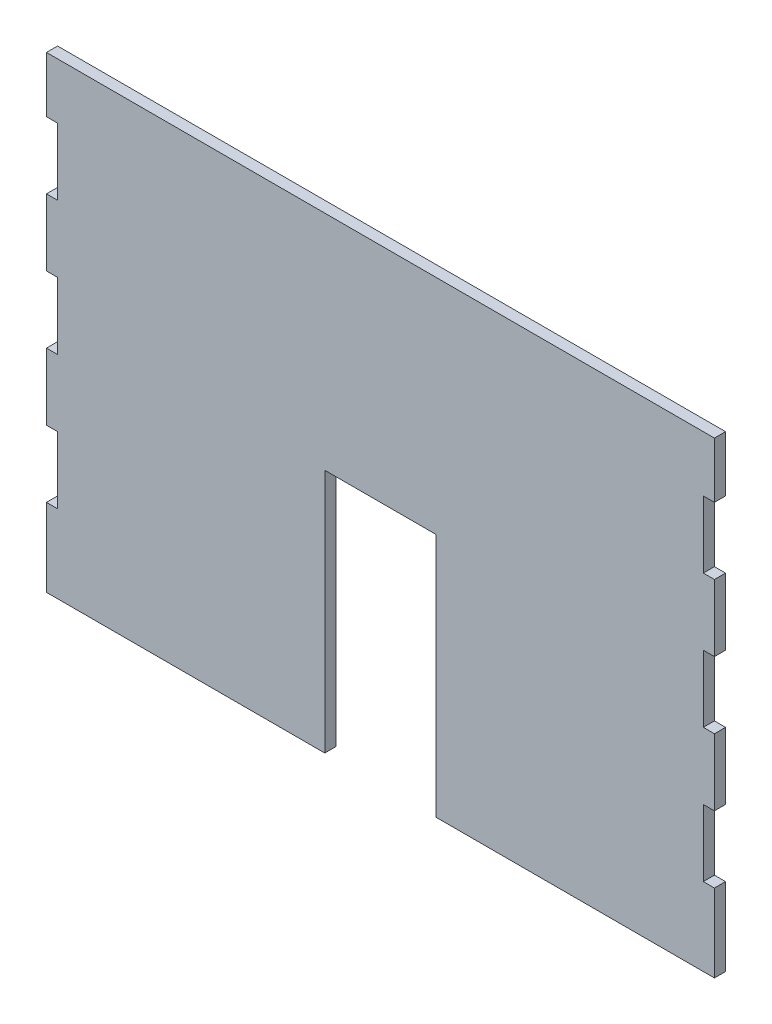
SolidWorks part; units mm, degrees
ref_plane "Front Plane" through (0, 0, 0) normal (0, 0, 1) x (1, 0, 0)
ref_plane "Top Plane" through (0, 0, 0) normal (0, 1, 0) x (1, 0, 0)
ref_plane "Right Plane" through (0, 0, 0) normal (1, 0, 0) x (0, 0, -1)
sketch "Sketch1" plane through (0, 0, 0) normal (0, 0, 1) x (1, 0, 0)
  line L1 (-150, 105) -> (150, 105)
  line L2 (-150, 105) -> (-150, -105)
  line L3 (-150, -105) -> (150, -105)
  line L4 (150, 105) -> (150, -105)
  line L5 (-150, 105) -> (150, -105) construction
  line L6 (-150, -105) -> (150, 105) construction
  point P0 (0, 0)
  dimension "D1" = 300
  dimension "D2" = 210
extrude "Boss-Extrude1" add sketch "Sketch1" along normal blind 5
sketch "Sketch2" plane through (0, 0, 0) normal (0, 0, -1) x (-1, 0, 0)
  line L0 (-150, 105) -> (150, 105) construction
  line L1 (-212.6198, 80) -> (-145, 80)
  line L2 (-212.6198, 80) -> (-212.6198, 50)
  line L3 (-212.6198, 50) -> (-145, 50)
  line L4 (-145, 80) -> (-145, 50)
  line L5 (-212.6198, 80) -> (-145, 50) construction
  line L6 (-212.6198, 50) -> (-145, 80) construction
  line L7 (-150, -105) -> (-150, 105) construction
  line L8 (-217.6198, 20) -> (-145, 20)
  line L9 (-217.6198, 20) -> (-217.6198, -10)
  line L10 (-217.6198, -10) -> (-145, -10)
  line L11 (-145, 20) -> (-145, -10)
  line L12 (-217.6198, 20) -> (-145, -10) construction
  line L13 (-217.6198, -10) -> (-145, 20) construction
  line L14 (-217.6198, -70) -> (-145, -70)
  line L15 (-217.6198, -70) -> (-217.6198, -40)
  line L16 (-217.6198, -40) -> (-145, -40)
  line L17 (-145, -70) -> (-145, -40)
  line L18 (-217.6198, -70) -> (-145, -40) construction
  line L19 (-217.6198, -40) -> (-145, -70) construction
  line L20 (150, 105) -> (150, -105) construction
  line L21 (145, 80) -> (198.2126, 80)
  line L22 (145, 80) -> (145, 50)
  line L23 (145, 50) -> (198.2126, 50)
  line L24 (198.2126, 80) -> (198.2126, 50)
  line L25 (145, 80) -> (198.2126, 50) construction
  line L26 (145, 50) -> (198.2126, 80) construction
  line L27 (145, 20) -> (217.6198, 20)
  line L28 (145, 20) -> (145, -10)
  line L29 (145, -10) -> (217.6198, -10)
  line L30 (217.6198, 20) -> (217.6198, -10)
  line L31 (145, 20) -> (217.6198, -10) construction
  line L32 (145, -10) -> (217.6198, 20) construction
  line L33 (145, -70) -> (217.6198, -70)
  line L34 (145, -70) -> (145, -40)
  line L35 (145, -40) -> (217.6198, -40)
  line L36 (217.6198, -70) -> (217.6198, -40)
  line L37 (145, -70) -> (217.6198, -40) construction
  line L38 (145, -40) -> (217.6198, -70) construction
  line L40 (150, 105) -> (150, -105) construction
  point P0 (-178.8099, 65)
  point P9 (-181.3099, 5)
  point P14 (-181.3099, -55)
  point P22 (171.6063, 65)
  point P27 (181.3099, 5)
  point P32 (181.3099, -55)
  dimension "D1" = 25
  dimension "D2" = 5
  dimension "D3" = 30
  dimension "D4" = 30
  dimension "D5" = 30
  dimension "D6" = 5
  dimension "D7" = 30
  dimension "D8" = 30
  dimension "D9" = 5
  dimension "D10" = 30
  dimension "D11" = 30
  dimension "D12" = 30
  dimension "D13" = 25
  dimension "D14" = 30
  dimension "D15" = 30
  dimension "D16" = 5
  dimension "D17" = 5
  dimension "D18" = 5
extrude "Cut-Extrude1" cut sketch "Sketch2" against normal through all
sketch "Sketch3" plane through (0, 0, 5) normal (0, 0, 1) x (1, 0, 0)
  line L0 (150, 20) -> (150, 50) construction
  line L1 (-25, 5) -> (25, 5)
  line L2 (-25, 5) -> (-25, -105)
  line L3 (-25, -105) -> (25, -105)
  line L4 (25, 5) -> (25, -105)
  line L5 (-25, 5) -> (25, -105) construction
  line L6 (-25, -105) -> (25, 5) construction
  line L7 (-150, -105) -> (150, -105) construction
  point P0 (0, -50)
  dimension "D1" = 50
  dimension "D2" = 110
  dimension "D3" = 125
  dimension "D4" = 0
extrude "Cut-Extrude2" cut sketch "Sketch3" against normal through all
